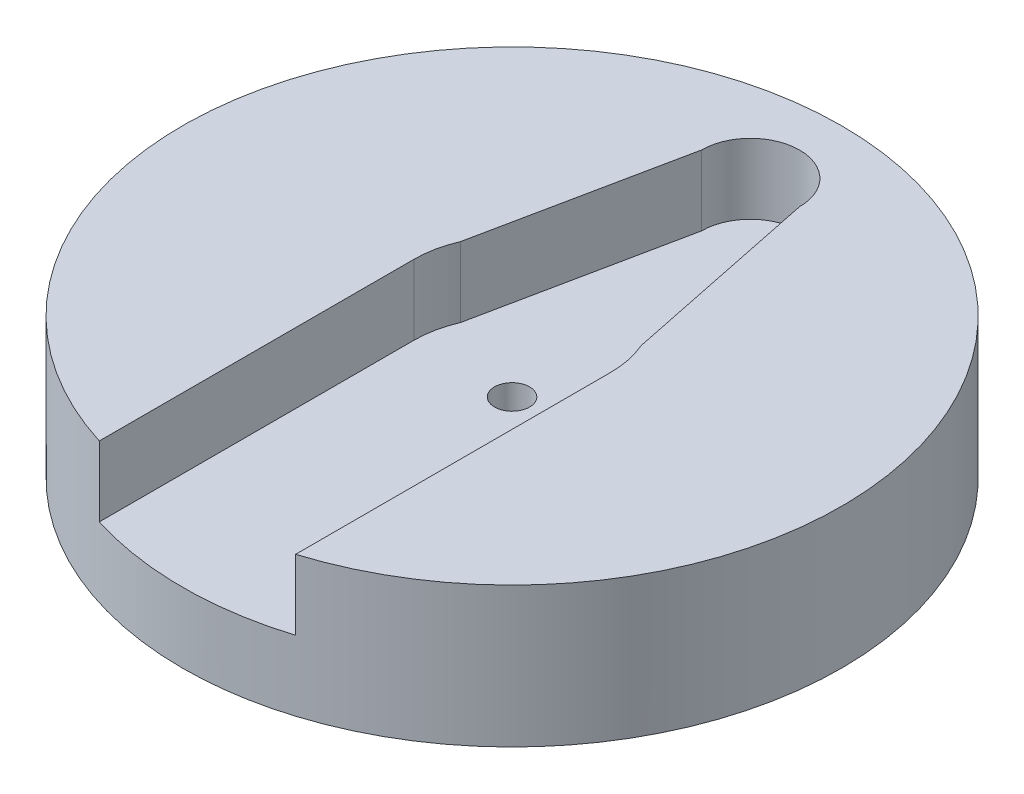
SolidWorks part; units mm, degrees
ref_plane "Alzado" through (0, 0, 0) normal (0, 0, 1) x (1, 0, 0)
ref_plane "Planta" through (0, 0, 0) normal (0, 1, 0) x (1, 0, 0)
ref_plane "Vista lateral" through (0, 0, 0) normal (1, 0, 0) x (0, 0, -1)
sketch "Croquis1" plane through (0, 0, 0) normal (0, 1, 0) x (1, 0, 0)
  circle A0 centre (0, 0) radius 23.5
  dimension "D1" = 47
extrude "Saliente-Extruir1" add sketch "Croquis1" along normal blind 10
sketch "Croquis2" plane through (0, 10, 0) normal (0, 1, 0) x (1, 0, 0)
  line L0 (-3.5, 17) -> (-7, 0)
  line L1 (-3.5, 17) -> (3.5, 17)
  line L2 (-3.5, 17) -> (-3.5, -17)
  line L3 (-3.5, -17) -> (3.5, -17)
  line L4 (3.5, 17) -> (3.5, -17)
  line L5 (-3.5, 17) -> (3.5, -17) construction
  line L6 (-3.5, -17) -> (3.5, 17) construction
  line L7 (3.5, 17) -> (7, 0)
  line L9 (-7, 0) -> (7, 0)
  line L10 (-7, 0) -> (-7, -23.5)
  line L11 (-7, -23.5) -> (7, -23.5)
  line L12 (7, 0) -> (7, -23.5)
  line L13 (-7, 0) -> (7, -23.5) construction
  line L14 (-7, -23.5) -> (7, 0) construction
  circle A0 centre (0, 0) radius 7
  circle A1 centre (0, 17) radius 3.5
  circle A4 centre (0, 0) radius 23.5 construction
  point P10 (0, -11.75)
  point P16 (0, -23.5)
  circle M10 centre (0, 0) radius 23.5
  dimension "D1" = 14
  dimension "D2" = 34
  dimension "D3" = 7
extrude "Cortar-Extruir3" cut sketch "Croquis2" against normal blind 5 contours L1 A1 | L1 A1 | A0 L2 L0 | A1 L2 A0 L4 | A0 L7 L4 | L7 A0 L4 L9 | L4 A0 L2 L9 | L2 A0 L0 L9 | L9 A0 L2 | L2 A0 L4 L9 | L4 A0 L9 | L7 A0 | L0 A0 | A0 L2 L3 L4 | A0 L4 L3 L2 L10 L12 M10
sketch "Croquis3" plane through (0, 10, 0) normal (0, 1, 0) x (1, 0, 0)
  circle A0 centre (0, 0) radius 1.25
  dimension "D1" = 2.5
extrude "Cortar-Extruir4" cut sketch "Croquis3" against normal up to surface (10 mm away) up to face at (0, 0, 23.5)
sketch "Croquis4" plane through (0, 0, 0) normal (1, 0, 0) x (0, 0, -1)
  line L1 (-23.5, 5) -> (23.5, 5)
  line L2 (-23.5, 5) -> (-23.5, 10)
  line L3 (-23.5, 10) -> (23.5, 10)
  line L4 (23.5, 5) -> (23.5, 10)
  line L5 (-20.5, 10) -> (20.5, 10)
  line L6 (-20.5, 10) -> (-20.5, 5)
  line L7 (-20.5, 5) -> (20.5, 5)
  line L8 (20.5, 10) -> (20.5, 5)
  line L9 (-20.5, 10) -> (20.5, 5) construction
  line L10 (-20.5, 5) -> (20.5, 10) construction
  line L11 (-30.5, 8) -> (-25.5, 8)
  line L12 (-30.5, 8) -> (-30.5, 6)
  line L13 (-30.5, 6) -> (-25.5, 6)
  line L14 (-25.5, 8) -> (-25.5, 6)
  line L15 (-30.5, 8) -> (-25.5, 6) construction
  line L16 (-30.5, 6) -> (-25.5, 8) construction
  point P6 (0, 7.5)
  point P13 (-28, 7)
  dimension "D1" = 41
  dimension "D2" = 1
  dimension "D3" = 5
  dimension "D4" = 2
  dimension "D5" = 5
extrude "Cortar-Extruir5" [suppressed] cut sketch "Croquis4" against normal through all and the other way through all contours L14 L11 L12 L13
sketch "Croquis5" plane through (0, 0, 0) normal (0, -1, 0) x (1, 0, 0)
  line L0 (-7.5, 0) -> (7.5, 0) construction
  line L1 (-7.5, 2.5) -> (7.5, 2.5)
  line L2 (-7.5, -2.5) -> (7.5, -2.5)
  arc A0 (-7.5, 2.5) -> (-7.5, -2.5) centre (-7.5, 0) ccw
  arc A1 (7.5, -2.5) -> (7.5, 2.5) centre (7.5, 0) ccw
  point P3 (0, 0)
  dimension "D1" = 2.5
  dimension "D2" = 15
extrude "Cortar-Extruir6" cut sketch "Croquis5" against normal blind 2
